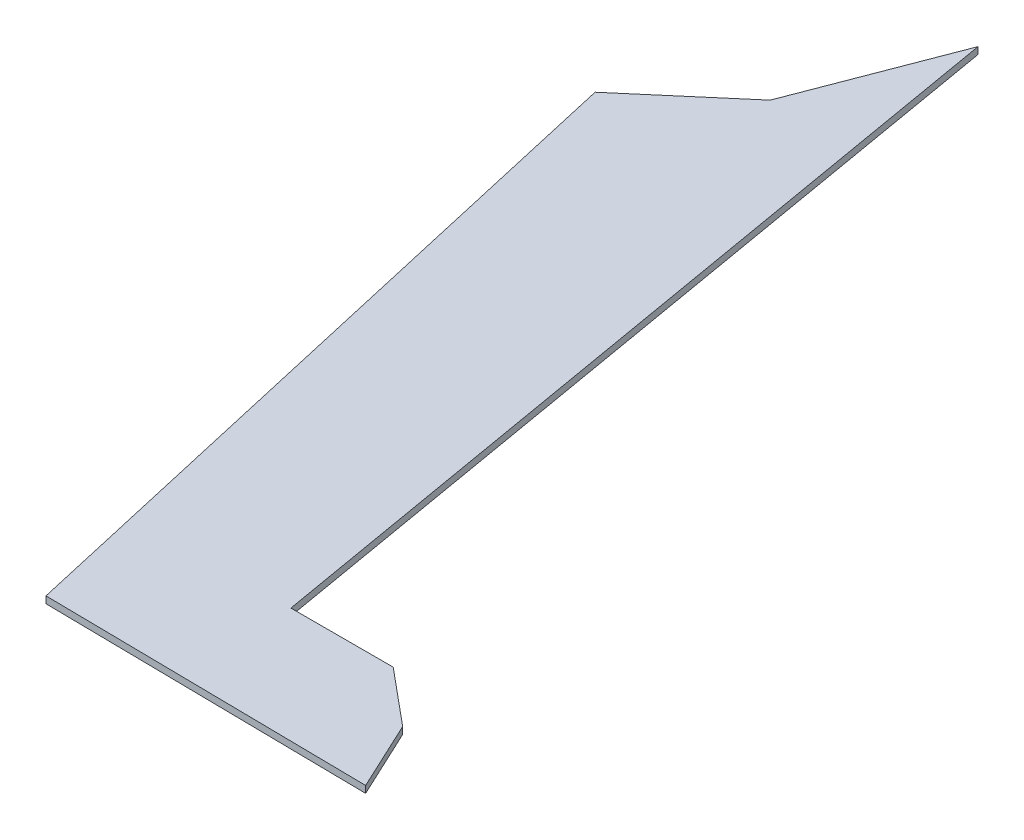
SolidWorks part; units mm, degrees
ref_plane "Plan de face" through (0, 0, 0) normal (0, 0, 1) x (1, 0, 0)
ref_plane "Plan de dessus" through (0, 0, 0) normal (0, 1, 0) x (1, 0, 0)
ref_plane "Plan de droite" through (0, 0, 0) normal (1, 0, 0) x (0, 0, -1)
sketch "Esquisse1" plane through (0, 0, 0) normal (0, 1, 0) x (1, 0, 0)
  line L0 (68.5103, 32.566) -> (38.7263, 32.566)
  line L1 (38.7263, 32.566) -> (-2.8122, 274.1356)
  line L2 (-2.8122, 274.1356) -> (-19.5662, 230.3871)
  line L3 (-19.5662, 230.3871) -> (-47.0522, 206.9012)
  line L4 (-47.0522, 206.9012) -> (0, 0)
  line L5 (0, 0) -> (94.3261, -1.276)
  line L8 (94.3261, -1.276) -> (84.8612, 18.9767)
  line L9 (84.8612, 18.9767) -> (68.5103, 32.566)
  point P7 (91.1397, 0)
  point P10 (0, 0)
  point P12 (0, 0)
  point P13 (93.9121, -1.276)
extrude "Boss.-Extru.1" add sketch "Esquisse1" along normal blind 2
